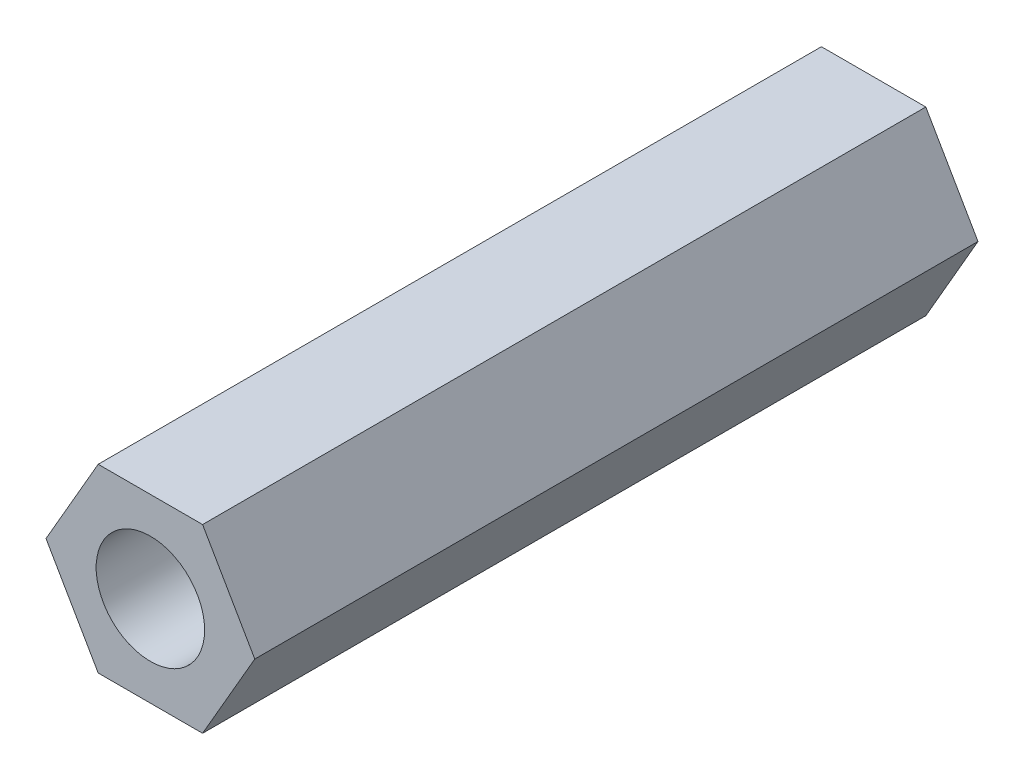
SolidWorks part; units mm, degrees
material "AISI 304"
ref_plane "前视基准面" through (0, 0, 0) normal (0, 0, 1) x (1, 0, 0)
ref_plane "上视基准面" through (0, 0, 0) normal (0, 1, 0) x (1, 0, 0)
ref_plane "右视基准面" through (0, 0, 0) normal (1, 0, 0) x (0, 0, -1)
sketch "草图1" plane through (0, 0, 0) normal (0, 0, 1) x (1, 0, 0)
  line L1 (1.4434, -2.5) -> (2.8868, 0)
  line L2 (2.8868, 0) -> (1.4434, 2.5)
  line L3 (1.4434, 2.5) -> (-1.4434, 2.5)
  line L4 (-1.4434, 2.5) -> (-2.8868, 0)
  line L5 (-2.8868, 0) -> (-1.4434, -2.5)
  line L6 (-1.4434, -2.5) -> (1.4434, -2.5)
  circle A0 centre (0, 0) radius 2.5 construction
  circle A1 centre (0, 0) radius 1.5
  dimension "D1" = 5
  dimension "D2" = 3
extrude "凸台-拉伸1" add sketch "草图1" along normal blind 20
